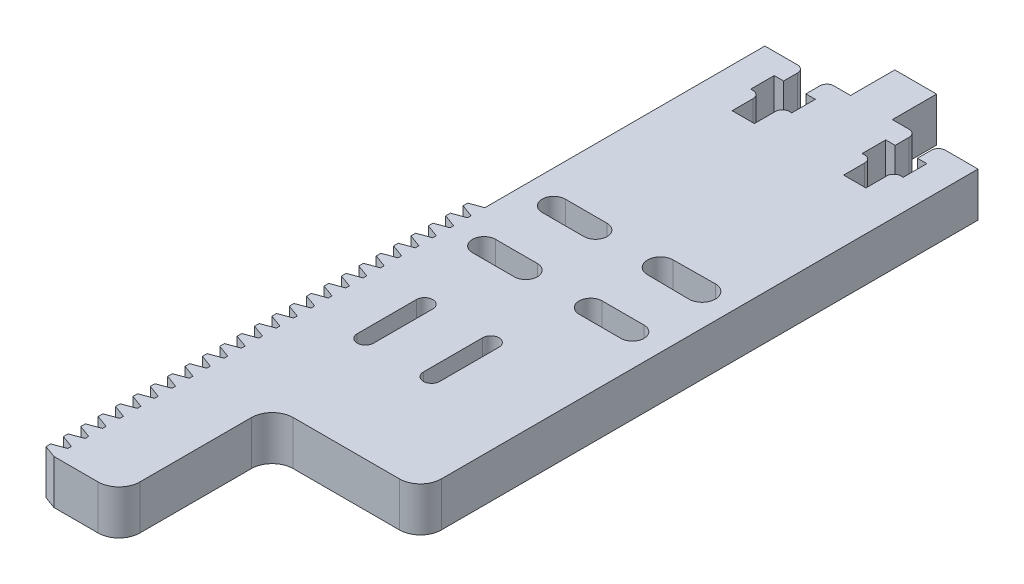
SolidWorks part; units mm, degrees
ref_plane "Front" through (0, 0, 0) normal (0, 0, 1) x (1, 0, 0)
ref_plane "Top" through (0, 0, 0) normal (0, 1, 0) x (1, 0, 0)
ref_plane "Right" through (0, 0, 0) normal (1, 0, 0) x (0, 0, -1)
ref_plane "Plane1" through (0, 6.35, 0) normal (0, 1, 0) x (1, 0, 0)
sketch "Sketch1" plane through (0, 6.35, 0) normal (0, 1, 0) x (1, 0, 0)
  line L0 (28.5248, 95.7792) -> (28.5248, 99.1496)
  line L1 (28.5248, 99.1496) -> (29.8748, 99.1496)
  line L2 (29.8748, 99.1496) -> (29.8748, 102.1496)
  line L3 (29.8748, 102.1496) -> (17.0748, 102.1496)
  line L4 (17.0748, 102.1496) -> (17.0748, 99.1496)
  line L5 (17.0748, 99.1496) -> (18.4248, 99.1496)
  line L6 (18.4248, 99.1496) -> (18.4248, 95.7732)
  line L7 (18.4248, 95.7732) -> (17.0748, 95.7732)
  line L8 (17.0748, 95.7732) -> (17.0748, 91.7592)
  line L9 (17.0748, 91.7592) -> (13.8748, 91.7592)
  line L10 (13.8748, 91.7592) -> (13.8748, 95.7732)
  line L11 (13.8748, 95.7732) -> (12.5248, 95.7732)
  line L12 (12.5248, 95.7732) -> (12.5248, 99.1496)
  line L13 (12.5248, 99.1496) -> (13.8748, 99.1496)
  line L14 (13.8748, 99.1496) -> (13.8748, 102.1496)
  line L15 (13.8748, 102.1496) -> (8.1857, 102.1496)
  line L16 (8.1857, 102.1496) -> (8.1857, 61.9707)
  line L17 (8.1857, 61.9707) -> (6.3887, 61.3167)
  line L18 (6.3887, 61.3167) -> (6.3887, 60.6476)
  line L19 (6.3887, 60.6476) -> (8.1857, 59.9936)
  line L20 (8.1857, 59.9936) -> (8.1857, 59.4772)
  line L21 (8.1857, 59.4772) -> (6.3887, 58.8232)
  line L22 (6.3887, 58.8232) -> (6.3887, 58.1541)
  line L23 (6.3887, 58.1541) -> (8.1857, 57.5001)
  line L24 (8.1857, 57.5001) -> (8.1857, 56.9837)
  line L25 (8.1857, 56.9837) -> (6.3887, 56.3297)
  line L26 (6.3887, 56.3297) -> (6.3887, 55.6606)
  line L27 (6.3887, 55.6606) -> (8.1857, 55.0066)
  line L28 (8.1857, 55.0066) -> (8.1857, 54.4902)
  line L29 (8.1857, 54.4902) -> (6.3887, 53.8362)
  line L30 (6.3887, 53.8362) -> (6.3887, 53.1671)
  line L31 (6.3887, 53.1671) -> (8.1857, 52.5131)
  line L32 (8.1857, 52.5131) -> (8.1857, 51.9967)
  line L33 (8.1857, 51.9967) -> (6.3887, 51.3427)
  line L34 (6.3887, 51.3427) -> (6.3887, 50.6736)
  line L35 (6.3887, 50.6736) -> (8.1857, 50.0196)
  line L36 (8.1857, 50.0196) -> (8.1857, 49.5032)
  line L37 (8.1857, 49.5032) -> (6.3887, 48.8492)
  line L38 (6.3887, 48.8492) -> (6.3887, 48.1801)
  line L39 (6.3887, 48.1801) -> (8.1857, 47.5261)
  line L40 (8.1857, 47.5261) -> (8.1857, 47.0097)
  line L41 (8.1857, 47.0097) -> (6.3887, 46.3557)
  line L42 (6.3887, 46.3557) -> (6.3887, 45.6866)
  line L43 (6.3887, 45.6866) -> (8.1857, 45.0326)
  line L44 (8.1857, 45.0326) -> (8.1857, 44.5162)
  line L45 (8.1857, 44.5162) -> (6.3887, 43.8622)
  line L46 (6.3887, 43.8622) -> (6.3887, 43.1931)
  line L47 (6.3887, 43.1931) -> (8.1857, 42.5391)
  line L48 (8.1857, 42.5391) -> (8.1857, 42.0227)
  line L49 (8.1857, 42.0227) -> (6.3887, 41.3687)
  line L50 (6.3887, 41.3687) -> (6.3887, 40.6996)
  line L51 (6.3887, 40.6996) -> (8.1857, 40.0456)
  line L52 (8.1857, 40.0456) -> (8.1857, 39.5292)
  line L53 (8.1857, 39.5292) -> (6.3887, 38.8752)
  line L54 (6.3887, 38.8752) -> (6.3887, 38.2061)
  line L55 (6.3887, 38.2061) -> (8.1857, 37.5521)
  line L56 (8.1857, 37.5521) -> (8.1857, 37.0357)
  line L57 (8.1857, 37.0357) -> (6.3887, 36.3817)
  line L58 (6.3887, 36.3817) -> (6.3887, 35.7126)
  line L59 (6.3887, 35.7126) -> (8.1857, 35.0586)
  line L60 (8.1857, 35.0586) -> (8.1857, 34.5422)
  line L61 (8.1857, 34.5422) -> (6.3887, 33.8882)
  line L62 (6.3887, 33.8882) -> (6.3887, 33.2191)
  line L63 (6.3887, 33.2191) -> (8.1857, 32.5651)
  line L64 (8.1857, 32.5651) -> (8.1857, 32.0487)
  line L65 (8.1857, 32.0487) -> (6.3887, 31.3947)
  line L66 (6.3887, 31.3947) -> (6.3887, 30.7256)
  line L67 (6.3887, 30.7256) -> (8.1857, 30.0716)
  line L68 (8.1857, 30.0716) -> (8.1857, 29.5552)
  line L69 (8.1857, 29.5552) -> (6.3887, 28.9012)
  line L70 (6.3887, 28.9012) -> (6.3887, 28.2321)
  line L71 (6.3887, 28.2321) -> (8.1857, 27.5781)
  line L72 (8.1857, 27.5781) -> (8.1857, 27.0617)
  line L73 (8.1857, 27.0617) -> (6.3887, 26.4077)
  line L74 (6.3887, 26.4077) -> (6.3887, 25.7386)
  line L75 (6.3887, 25.7386) -> (8.1857, 25.0846)
  line L76 (8.1857, 25.0846) -> (8.1857, 24.5682)
  line L77 (8.1857, 24.5682) -> (6.3887, 23.9142)
  line L78 (6.3887, 23.9142) -> (6.3887, 23.2451)
  line L79 (6.3887, 23.2451) -> (8.1857, 22.5911)
  line L80 (8.1857, 22.5911) -> (8.1857, 22.0747)
  line L81 (8.1857, 22.0747) -> (6.3887, 21.4207)
  line L82 (6.3887, 21.4207) -> (6.3887, 20.7516)
  line L83 (6.3887, 20.7516) -> (8.1857, 20.0976)
  line L84 (8.1857, 20.0976) -> (8.1857, 19.5812)
  line L85 (8.1857, 19.5812) -> (6.3887, 18.9272)
  line L86 (6.3887, 18.9272) -> (6.3887, 18.2581)
  line L87 (6.3887, 18.2581) -> (8.1857, 17.6041)
  line L88 (8.1857, 17.6041) -> (8.1857, 17.0877)
  line L89 (8.1857, 17.0877) -> (6.3887, 16.4337)
  line L90 (6.3887, 16.4337) -> (6.3887, 15.7646)
  line L91 (6.3887, 15.7646) -> (8.1857, 15.1106)
  line L92 (8.1857, 15.1106) -> (8.1857, 14.5942)
  line L93 (8.1857, 14.5942) -> (6.3887, 13.9402)
  line L94 (6.3887, 13.9402) -> (6.3887, 13.2711)
  line L95 (6.3887, 13.2711) -> (8.1857, 12.6171)
  line L96 (8.1857, 12.6171) -> (8.1857, 12.1007)
  line L97 (8.1857, 12.1007) -> (6.3887, 11.4467)
  line L98 (6.3887, 11.4467) -> (6.3887, 10.7776)
  line L99 (6.3887, 10.7776) -> (8.1857, 10.1236)
  line L100 (8.1857, 10.1236) -> (8.1857, 9.6072)
  line L101 (8.1857, 9.6072) -> (6.3887, 8.9532)
  line L102 (6.3887, 8.9532) -> (6.3887, 8.2841)
  line L103 (6.3887, 8.2841) -> (8.1857, 7.6301)
  line L104 (8.1857, 7.6301) -> (8.1857, 7.1137)
  line L105 (8.1857, 7.1137) -> (6.3887, 6.4597)
  line L106 (6.3887, 6.4597) -> (6.3887, 5.7906)
  line L107 (6.3887, 5.7906) -> (8.1857, 5.1366)
  line L108 (8.1857, 5.1366) -> (8.1857, 4.6202)
  line L109 (8.1857, 4.6202) -> (6.3887, 3.9662)
  line L110 (6.3887, 3.9662) -> (6.3887, 3.2971)
  line L111 (6.3887, 3.2971) -> (8.1857, 2.6431)
  line L112 (8.1857, 2.6431) -> (8.1857, 2.1267)
  line L113 (8.1857, 2.1267) -> (6.3887, 1.4727)
  line L114 (6.3887, 1.4727) -> (6.3887, 0.8036)
  line L115 (6.3887, 0.8036) -> (8.1857, 0.1496)
  line L116 (8.1857, 0.1496) -> (14.5138, 0.1496)
  line L117 (17.5138, 3.1496) -> (17.5138, 22.1496)
  line L118 (17.5138, 22.1496) -> (35.7638, 22.1496)
  line L119 (38.7638, 25.1496) -> (38.7638, 102.1496)
  line L120 (38.7638, 102.1496) -> (33.0748, 102.1496)
  line L121 (33.0748, 102.1496) -> (33.0748, 99.1496)
  line L122 (33.0748, 99.1496) -> (34.4248, 99.1496)
  line L123 (34.4248, 99.1496) -> (34.4248, 95.7532)
  line L124 (34.4248, 95.7532) -> (33.0748, 95.7592)
  line L125 (33.0748, 95.7592) -> (33.0748, 91.7592)
  line L126 (33.0748, 91.7592) -> (29.8748, 91.7592)
  line L127 (29.8748, 91.7592) -> (29.8748, 95.7732)
  line L128 (29.8748, 95.7732) -> (28.5248, 95.7792)
  arc A0 (14.5138, 0.1496) -> (17.5138, 3.1496) centre (14.5138, 3.1496) ccw
  arc A1 (35.7638, 22.1496) -> (38.7638, 25.1496) centre (35.7638, 25.1496) ccw
extrude "Boss-Extrude1" add sketch "Sketch1" against normal blind 6.35
sketch "Sketch2" plane through (0, 6.35, 0) normal (0, 1, 0) x (-1, 0, 0)
  line L0 (-24.1888, -45.6496) -> (-24.1888, -37.1496)
  line L1 (-26.5388, -37.1496) -> (-26.5388, -45.6496)
  arc A0 (-26.5388, -45.6496) -> (-24.1888, -45.6496) centre (-25.3638, -45.6496) ccw
  arc A1 (-24.1888, -37.1496) -> (-26.5388, -37.1496) centre (-25.3638, -37.1496) ccw
extrude "Cut-Extrude1" cut sketch "Sketch2" against normal through all
sketch "Sketch3" plane through (0, 6.35, 0) normal (0, 1, 0) x (-1, 0, 0)
  line L0 (-12.8874, -55.4916) -> (-18.8874, -55.4916)
  line L1 (-18.8874, -58.8076) -> (-12.8874, -58.8076)
  arc A0 (-12.8874, -58.8076) -> (-12.8874, -55.4916) centre (-12.8874, -57.1496) ccw
  arc A1 (-18.8874, -55.4916) -> (-18.8874, -58.8076) centre (-18.8874, -57.1496) ccw
extrude "Cut-Extrude2" cut sketch "Sketch3" against normal through all
sketch "Sketch4" plane through (0, 6.35, 0) normal (0, 1, 0) x (-1, 0, 0)
  line L0 (-18.8874, -68.8077) -> (-12.8874, -68.8077)
  line L1 (-12.8874, -65.4914) -> (-18.8874, -65.4914)
  arc A0 (-18.8874, -65.4914) -> (-18.8874, -68.8077) centre (-18.8874, -67.1496) ccw
  arc A1 (-12.8874, -68.8077) -> (-12.8874, -65.4914) centre (-12.8874, -67.1496) ccw
extrude "Cut-Extrude3" cut sketch "Sketch4" against normal through all
sketch "Sketch5" plane through (0, 6.35, 0) normal (0, 1, 0) x (-1, 0, 0)
  line L0 (-28.1867, -55.4916) -> (-34.1867, -55.4916)
  line L1 (-34.1867, -58.8076) -> (-28.1867, -58.8076)
  arc A0 (-28.1867, -58.8076) -> (-28.1867, -55.4916) centre (-28.1867, -57.1496) ccw
  arc A1 (-34.1867, -55.4916) -> (-34.1867, -58.8076) centre (-34.1867, -57.1496) ccw
extrude "Cut-Extrude4" cut sketch "Sketch5" against normal through all
sketch "Sketch6" plane through (0, 6.35, 0) normal (0, 1, 0) x (-1, 0, 0)
  line L0 (-28.168, -65.3092) -> (-34.1674, -65.248)
  line L1 (-34.1674, -69.0511) -> (-28.168, -68.99)
  arc A0 (-28.168, -68.99) -> (-28.168, -65.3092) centre (-28.1867, -67.1496) ccw
  arc A1 (-34.1674, -65.248) -> (-34.1674, -69.0511) centre (-34.1867, -67.1496) ccw
extrude "Cut-Extrude5" cut sketch "Sketch6" against normal through all
sketch "Sketch7" plane through (0, 0, 0) normal (0, -1, 0) x (1, 0, 0)
  line L0 (14.6875, -37.1496) -> (14.6875, -45.6496)
  line L1 (17.0375, -45.6496) -> (17.0375, -37.1496)
  arc A0 (17.0375, -37.1496) -> (14.6875, -37.1496) centre (15.8625, -37.1496) ccw
  arc A1 (14.6875, -45.6496) -> (17.0375, -45.6496) centre (15.8625, -45.6496) ccw
extrude "Cut-Extrude6" cut sketch "Sketch7" against normal through all
fillet "Fillet1" radius 1 8 edges at (17.0748, 3.175, -102.1496) (13.8748, 3.175, -102.1496) (13.8748, 3.175, -95.7732) (17.0748, 3.175, -95.7732) (29.8748, 3.175, -102.1496) (29.8748, 3.175, -95.7732) (33.0748, 3.175, -95.7592) (33.0748, 3.175, -102.1496)
fillet "Fillet2" radius 3 1 edges at (17.5138, 3.175, -22.1496)
sketch "Sketch8" plane through (0, 6.35, 0) normal (0, 1, 0) x (1, 0, 0)
  line L0 (23.4748, 102.1496) -> (23.4748, 105.3246) construction
  line L1 (28.8748, 102.1496) -> (18.0748, 102.1496) construction
  line L3 (26.4748, 108.4996) -> (20.4748, 108.4996)
  line L4 (26.4748, 108.4996) -> (26.4748, 102.1496)
  line L5 (26.4748, 102.1496) -> (20.4748, 102.1496)
  line L6 (20.4748, 108.4996) -> (20.4748, 102.1496)
  line L7 (26.4748, 108.4996) -> (20.4748, 102.1496) construction
  line L8 (26.4748, 102.1496) -> (20.4748, 108.4996) construction
  dimension "D1" = 6.35
  dimension "D2" = 6
extrude "Boss-Extrude2" add sketch "Sketch8" against normal up to surface (6.35 mm away) up to face at (15.8625, 0, -41.3996)
